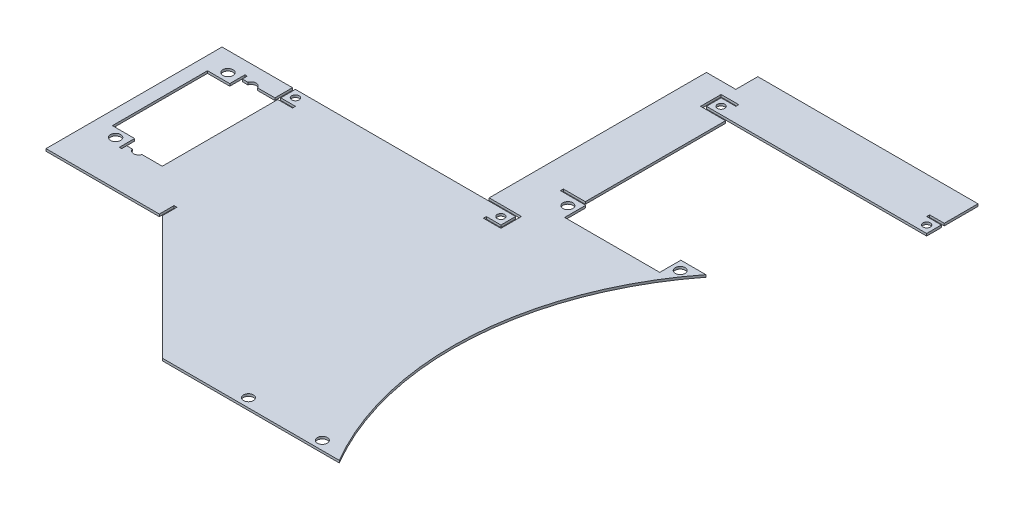
SolidWorks part; units mm, degrees
ref_plane "Front Plane" through (0, 0, 0) normal (0, 0, 1) x (1, 0, 0)
ref_plane "Top Plane" through (0, 0, 0) normal (0, 1, 0) x (1, 0, 0)
ref_plane "Right Plane" through (0, 0, 0) normal (1, 0, 0) x (0, 0, -1)
sketch "Sketch2" plane through (0, 0, 0) normal (0, 1, 0) x (1, 0, 0)
  line L1 (-127, -127) -> (127, -127)
  line L2 (-127, -127) -> (-127, 127)
  line L3 (-127, 127) -> (127, 127)
  line L4 (127, -127) -> (127, 127)
  line L5 (-127, -127) -> (127, 127) construction
  line L6 (-127, 127) -> (127, -127) construction
  point P0 (0, 0)
  dimension "D1" = 254
  dimension "D2" = 254
extrude "Boss-Extrude1" add sketch "Sketch2" along normal blind 1.0008 contours L3 L4 L1 L2
ref_plane "Plane1" through (127, 0, 0) normal (1, 0, 0) x (0, 0, -1)
sketch "Sketch3" plane through (0, 1.0008, 0) normal (0, 1, 0) x (1, 0, 0)
  line L0 (63.5, 41.91) -> (63.5, 3.81) construction
  line L1 (127, 47.252) -> (57.15, 47.252)
  line L2 (127, 47.252) -> (127, 21.852)
  line L3 (127, 21.852) -> (57.15, 21.852)
  line L4 (57.15, 47.252) -> (57.15, 21.852)
  line L7 (64.096, 22.36) -> (70.7, 22.36) construction
  line L8 (64.096, 22.36) -> (70.7, 22.36) construction
  dimension "D1" = 6.35
  dimension "D2" = 0.508
  dimension "D3" = 25.4
extrude "Cut-Extrude1" cut sketch "Sketch3" against normal through all both and the other way through all
sketch "Sketch4" plane through (0, 1.0008, 0) normal (0, 1, 0) x (1, 0, 0)
  line L4 (57.15, 21.852) -> (57.15, 47.252)
  line L5 (127, 127) -> (-127, 127)
  line L6 (127, -127) -> (127, 21.852)
  line L8 (127, 21.852) -> (57.15, 21.852)
  line L11 (-127, -127) -> (127, -127)
  line L12 (127, -127) -> (127, 21.852)
  line L17 (112.9689, -127) -> (127, -127)
  line L18 (127, 21.852) -> (122.64, 21.852)
  line L21 (-127, 127) -> (-127, -127)
  line L22 (57.15, 47.252) -> (127, 47.252)
  line L23 (127, 47.252) -> (127, 127)
  arc A0 (127, 27.1603) -> (114.5024, -129.54) centre (227.33, -59.69) ccw construction
  arc A1 (122.64, 21.852) -> (112.9689, -127) centre (227.33, -59.69) ccw
  dimension "D1" = 0
extrude "Cut-Extrude2" cut sketch "Sketch4" against normal through all both
sketch "Sketch5" plane through (0, 1.0008, 0) normal (0, 1, 0) x (1, 0, 0)
  line L0 (63.5, -129.54) -> (63.5, -61.2891) construction
  circle A0 centre (115.577, 17.86) radius 2.1 construction
  circle A1 centre (66.977, 17.86) radius 2.1 construction
  circle A2 centre (115.577, 17.86) radius 2.1 construction
  circle A3 centre (66.977, 17.86) radius 2.1 construction
  circle A4 centre (69.85, -123.19) radius 2.15
  circle A5 centre (101.8024, -123.19) radius 2.15
  circle A6 centre (66.977, 17.86) radius 2.15
  circle A7 centre (115.577, 17.86) radius 2.15
  dimension "D1" = 6.35
  dimension "D5" = 4.3
  dimension "D2" = 12.7
  dimension "D3" = 6.35
  dimension "D4" = 6.35
extrude "Cut-Extrude3" cut sketch "Sketch5" against normal through all both
sketch "Sketch6" plane through (0, 1.0008, 0) normal (0, 1, 0) x (1, 0, 0)
  line L12 (70.7, 22.36) -> (70.7, 12.733)
  line L13 (70.7, 12.733) -> (111.854, 12.733)
  line L14 (111.854, 12.733) -> (111.854, 22.36)
  line L15 (111.854, 22.36) -> (118.458, 22.36)
  line L16 (118.458, 22.36) -> (118.458, 23.36)
  line L17 (118.458, 23.36) -> (111.854, 23.36)
  line L18 (111.854, 23.36) -> (111.854, 32.987)
  line L19 (111.854, 32.987) -> (70.7, 32.987)
  line L20 (70.7, 32.987) -> (70.7, 23.36)
  line L21 (70.7, 23.36) -> (64.096, 23.36)
  line L22 (64.096, 23.36) -> (64.096, 22.36)
  line L23 (64.096, 22.36) -> (70.7, 22.36)
  line L24 (70.7, 22.36) -> (70.7, 12.733)
  line L25 (70.7, 12.733) -> (111.854, 12.733)
  line L26 (111.854, 12.733) -> (111.854, 22.36)
  line L27 (111.854, 22.36) -> (118.458, 22.36)
  line L28 (118.458, 22.36) -> (118.458, 23.36)
  line L29 (118.458, 23.36) -> (111.854, 23.36)
  line L30 (111.854, 23.36) -> (111.854, 32.987)
  line L31 (111.854, 32.987) -> (70.7, 32.987)
  line L32 (70.7, 32.987) -> (70.7, 23.36)
  line L33 (70.7, 23.36) -> (64.096, 23.36)
  line L34 (64.096, 23.36) -> (64.096, 22.36)
  line L35 (64.096, 22.36) -> (70.7, 22.36)
  circle A1 centre (66.977, 27.86) radius 2.1
  circle A2 centre (66.977, 27.86) radius 2.1
  circle A3 centre (66.977, 17.86) radius 2.1
  circle A4 centre (66.977, 17.86) radius 2.1
  circle A5 centre (115.577, 27.86) radius 2.1
  circle A6 centre (115.577, 27.86) radius 2.1
  circle A7 centre (115.577, 17.86) radius 2.1
  circle A8 centre (115.577, 17.86) radius 2.1
  dimension "D1" = 0
  dimension "D2" = 0
  dimension "D3" = 0
  dimension "D4" = 0
  dimension "D5" = 0
extrude "Cut-Extrude4" cut sketch "Sketch6" against normal through all both
sketch "Sketch7" plane through (0, 1.0008, 0) normal (0, 1, 0) x (1, 0, 0)
  line L1 (-35.5092, 2.4892) -> (59.7408, 2.4892)
  line L2 (-35.5092, 2.4892) -> (-35.5092, 97.7392)
  line L3 (-35.5092, 97.7392) -> (59.7408, 97.7392)
  line L4 (59.7408, 2.4892) -> (59.7408, 97.7392)
  line L5 (-35.5092, 2.4892) -> (59.7408, 97.7392) construction
  line L6 (-35.5092, 97.7392) -> (59.7408, 2.4892) construction
  circle A2 centre (101.6, 22.86) radius 4.7625 construction
  circle A3 centre (101.6, 22.86) radius 4.699 construction
  point P0 (12.1158, 50.1142)
  dimension "D1" = 95.25
  dimension "D3" = 20.3708
  dimension "D2" = 137.1092
extrude "Cut-Extrude5" cut sketch "Sketch7" against normal through all both
sketch "Sketch8" plane through (0, 1.0008, 0) normal (0, 1, 0) x (1, 0, 0)
  line L0 (127, 47.252) -> (127, 127)
  line L2 (127, 127) -> (-127, 127)
  line L3 (-127, 127) -> (-127, -127)
  line L4 (-127, -127) -> (-35.5092, -127)
  line L5 (-127, -127) -> (112.9689, -127) construction
  line L6 (-35.5092, -127) -> (-35.5092, 47.252)
  line L7 (-35.5092, 47.252) -> (127, 47.252)
  line L9 (-35.5092, 97.7392) -> (-35.5092, 2.4892) construction
extrude "Cut-Extrude6" cut sketch "Sketch8" against normal through all both
sketch "Sketch17" plane through (0, 1.0008, 0) normal (0, 1, 0) x (1, 0, 0)
  line L1 (59.7408, 2.4892) -> (47.0408, 2.4892)
  line L2 (59.7408, 2.4892) -> (59.7408, 85.0392)
  line L3 (59.7408, 97.7392) -> (47.0408, 97.7392)
  line L4 (47.0408, 2.4892) -> (47.0408, 97.7392)
  line L5 (-35.5092, 2.4892) -> (59.7408, 2.4892) construction
  line L6 (59.7408, 97.7392) -> (154.9908, 97.7392)
  line L8 (59.7408, 85.0392) -> (154.9908, 85.0392)
  line L9 (154.9908, 97.7392) -> (154.9908, 85.0392)
  dimension "D1" = 12.7
extrude "Boss-Extrude4" add sketch "Sketch17" against normal up to surface (1.0008 mm away) up to face at (62.6286, 0, 13.466)
sketch "Sketch18" plane through (0, 1.0008, 0) normal (0, 1, 0) x (1, 0, 0)
  line L0 (47.0408, 2.4892) -> (59.7408, 2.4892)
extrude "Cut-Extrude-Thin4" cut sketch "Sketch18" against normal through all both and the other way through all thin thin type one direction reverse wall 1.27
sketch "Sketch9" plane through (0, 1.0008, 0) normal (0, 1, 0) x (1, 0, 0)
  line L0 (-35.5092, -55.1138) -> (36.377, -127)
  line L1 (-35.5092, -127) -> (-35.5092, 2.4892) construction
  line L2 (-35.5092, -127) -> (112.9689, -127) construction
  line L3 (-35.5092, -127) -> (36.377, -127)
  line L4 (-35.5092, -127) -> (-35.5092, -55.1138)
  circle A0 centre (101.727, 22.86) radius 145.8265 construction
  circle A1 centre (101.727, 22.86) radius 152.1765 construction
  dimension "D1" = 6.35
  dimension "D2" = 45
extrude "Cut-Extrude7" cut sketch "Sketch9" against normal through all both
sketch "Sketch10" plane through (0, 1.0008, 0) normal (0, 1, 0) x (1, 0, 0)
  line L37 (59.7408, 21.852) -> (59.7408, 85.0392) construction
  line L38 (59.7408, 83.7692) -> (69.2658, 83.7692)
  line L39 (59.7408, 83.7692) -> (59.7408, 23.122)
  line L40 (59.7408, 23.122) -> (69.2658, 23.122)
  line L41 (69.2658, 83.7692) -> (69.2658, 23.122)
  line L42 (70.7, 21.852) -> (59.7408, 21.852) construction
  line L43 (59.7408, 85.0392) -> (154.9908, 85.0392) construction
  line L44 (154.9908, 97.7392) -> (47.0408, 97.7392) construction
  line L45 (59.7408, 97.7392) -> (154.9908, 97.7392)
  line L46 (59.7408, 97.7392) -> (59.7408, 107.2642)
  line L47 (59.7408, 107.2642) -> (154.9908, 107.2642)
  line L48 (154.9908, 97.7392) -> (154.9908, 107.2642)
  dimension "D1" = 1.27
  dimension "D2" = 1.27
  dimension "D3" = 9.525
extrude "Boss-Extrude2" add sketch "Sketch10" against normal up to surface (1.0008 mm away) up to face at (69.7769, 0, -10.7824)
sketch "Sketch14" plane through (0, 1.0008, 0) normal (0, 1, 0) x (1, 0, 0)
  line L0 (-61.5112, -9.5453) -> (-41.2572, -50.6993) construction
  line L5 (-61.5112, -9.5453) -> (-51.8842, -9.5453)
  line L6 (-61.5112, -9.5453) -> (-61.5112, -50.6993)
  line L7 (-61.5112, -50.6993) -> (-51.8842, -50.6993)
  line L12 (-41.2572, -9.5453) -> (-41.2572, -50.6993)
  line L17 (-35.5092, -5.1308) -> (-67.2592, -5.1308)
  line L22 (-35.5092, -55.1138) -> (-35.5092, 2.4892) construction
  line L23 (-67.2592, -5.1308) -> (-67.2592, -55.1138)
  line L24 (-67.2592, -55.1138) -> (-35.5092, -55.1138)
  line L25 (-35.5092, -55.1138) -> (-35.5092, -5.1308)
  line L34 (-41.2572, -9.5453) -> (-61.5112, -50.6993) construction
  line L35 (-56.3842, -5.8223) -> (-46.3842, -54.4223) construction
  line L36 (-56.3842, -54.4223) -> (-46.3842, -5.8223) construction
  line L37 (-50.8842, -50.6993) -> (-41.2572, -50.6993)
  line L38 (-51.8842, -50.6993) -> (-51.8842, -57.3033)
  line L39 (-51.8842, -57.3033) -> (-50.8842, -57.3033)
  line L40 (-50.8842, -50.6993) -> (-50.8842, -57.3033)
  line L41 (-51.3842, -30.1223) -> (-15.6253, -30.1223) construction
  line L42 (-51.8842, -2.9413) -> (-50.8842, -2.9413)
  line L43 (-51.8842, -9.5453) -> (-51.8842, -2.9413)
  line L44 (-50.8842, -9.5453) -> (-50.8842, -2.9413)
  line L45 (-50.8842, -9.5453) -> (-41.2572, -9.5453)
  line L47 (-67.2592, -5.1308) -> (-67.2592, 2.4892)
  line L48 (-67.2592, 2.4892) -> (-35.5092, 2.4892)
  line L49 (-35.5092, 2.4892) -> (-35.5092, -5.1308)
  line L51 (-35.5092, 2.4892) -> (59.7408, 2.4892) construction
  line L52 (-67.2592, -55.1138) -> (-67.2592, -73.66)
  line L53 (-67.2592, -73.66) -> (-16.963, -73.66)
  line L54 (36.377, -127) -> (-35.5092, -55.1138) construction
  line L57 (-16.963, -73.66) -> (-35.5092, -55.1138)
  circle A8 centre (-56.3842, -54.4223) radius 2.2
  circle A9 centre (-46.3842, -54.4223) radius 2.2
  circle A10 centre (-56.3842, -5.8223) radius 2.2
  circle A11 centre (-46.3842, -5.8223) radius 2.2
  point P9 (-51.3842, -57.3033)
  point P19 (-51.3842, -30.1223)
  point P20 (-51.3842, -30.1223)
  point P37 (-67.2592, -30.1223)
  point P39 (-51.3842, -55.1138)
  dimension "D3" = 48.6
  dimension "D4" = 4.4
  dimension "D2" = 10
  dimension "D5" = 41.154
  dimension "D6" = 20.254
  dimension "D7" = 1
  dimension "D8" = 6.604
  dimension "D9" = 31.75
  dimension "D10" = 7.62
  dimension "D11" = 53.34
extrude "Boss-Extrude3" add sketch "Sketch14" against normal up to surface (1.0008 mm away)
sketch "Sketch15" plane through (0, 1.0008, 0) normal (0, 1, 0) x (1, 0, 0)
  line L0 (-16.963, -73.66) -> (-16.963, -67.31)
  dimension "D1" = 6.35
extrude "Cut-Extrude-Thin3" cut sketch "Sketch15" against normal through all both and the other way through all thin thin type one direction reverse wall 1.27
sketch "Sketch19" plane through (0, 1.0008, 0) normal (0, 1, 0) x (1, 0, 0)
  line L0 (154.9908, 85.0392) -> (154.9908, 107.2642) construction
  line L1 (59.7408, 85.0392) -> (154.9908, 85.0392) construction
  line L2 (59.7408, 83.7692) -> (59.7408, 85.0392) construction
  line L3 (-67.2592, 2.4892) -> (59.7408, 2.4892) construction
  line L4 (59.7408, 2.4892) -> (59.7408, 3.7592) construction
  line L5 (62.9158, 88.2142) -> (151.8158, 88.2142) construction
  line L6 (-32.3342, -0.6858) -> (56.5658, -0.6858) construction
  circle A0 centre (56.5658, -0.6858) radius 1.5875
  circle A1 centre (-32.3342, -0.6858) radius 1.5875
  circle A2 centre (151.8158, 88.2142) radius 1.5875
  circle A3 centre (62.9158, 88.2142) radius 1.5875
  dimension "D3" = 3.175
  dimension "D1" = 3.175
  dimension "D2" = 3.175
  dimension "D4" = 3.175
  dimension "D5" = 3.175
  dimension "D6" = 3.175
extrude "Cut-Extrude8" cut sketch "Sketch19" against normal through all both and the other way through all
sketch "Sketch20" plane through (0, 1.0008, 0) normal (0, 1, 0) x (1, 0, 0)
  line L0 (-35.5092, 2.4892) -> (-35.5092, -3.8608)
  line L1 (-67.2592, 2.4892) -> (59.7408, 2.4892) construction
  line L2 (-35.5092, -3.8608) -> (-29.1592, -3.8608)
  line L3 (59.7408, 2.4892) -> (59.7408, -3.8608)
  line L4 (59.7408, -3.8608) -> (53.3908, -3.8608)
  line L5 (59.7408, 85.0392) -> (59.7408, 91.3892)
  line L6 (59.7408, 91.3892) -> (66.0908, 91.3892)
  line L7 (154.9908, 91.3892) -> (154.9908, 85.0392) construction
  line L8 (148.6408, 91.3892) -> (154.9908, 91.3892)
  line L9 (154.9908, 85.0392) -> (154.9908, 107.2642) construction
  line L10 (58.4708, 85.0392) -> (58.4708, 92.6592)
  line L11 (58.4708, 92.6592) -> (66.0908, 92.6592)
  line L12 (148.6408, 92.6592) -> (154.9908, 92.6592)
  line L13 (61.0108, 2.4892) -> (61.0108, -5.1308)
  line L14 (61.0108, -5.1308) -> (53.3908, -5.1308)
  line L15 (-36.7792, 2.4892) -> (-36.7792, -5.1308)
  line L16 (-36.7792, -5.1308) -> (-29.1592, -5.1308)
  line L17 (-36.7792, 2.4892) -> (-35.5092, 2.4892)
  line L18 (-29.1592, -3.8608) -> (-29.1592, -5.1308)
  line L19 (148.6408, 92.6592) -> (148.6408, 91.3892)
  line L20 (154.9908, 91.3892) -> (154.9908, 92.6592)
  line L21 (59.7408, 85.0392) -> (58.4708, 85.0392)
  line L22 (66.0908, 91.3892) -> (66.0908, 92.6592)
  line L23 (59.7408, 2.4892) -> (61.0108, 2.4892)
  line L24 (53.3908, -3.8608) -> (53.3908, -5.1308)
  line L25 (59.7408, 85.0392) -> (59.7408, 83.7692)
  line L26 (59.7408, 83.7692) -> (69.2658, 83.7692) construction
  line L27 (59.7408, 83.7692) -> (58.4708, 83.7692)
  line L28 (58.4708, 83.7692) -> (58.4708, 85.0392)
  line L29 (59.7408, 2.4892) -> (59.7408, 3.7592)
  line L30 (59.7408, 3.7592) -> (61.0108, 3.7592)
  line L31 (61.0108, 3.7592) -> (61.0108, 2.4892)
  dimension "D1" = 6.35
  dimension "D2" = 95.25
  dimension "D3" = 1.27
  dimension "D4" = 1.27
extrude "Cut-Extrude12" cut sketch "Sketch20" against normal through all both contours L28 L27 L25 L21 | L6 L22 L11 L10 L21 L5 | L31 L30 L29 L23 | L4 L24 L14 L13 L23 L3 | L18 L2 L0 L17 L15 L16 | L8 L20 L12 L19
equation "\"looseTol\"= 0.02in"
equation "\"tightTol\"= 0.005in"
equation "\"normTol\"= 0.01in"
equation "\"D2@Sketch3\"=\"looseTol\""
equation "\"D5@Sketch5\"=4.3mm"
